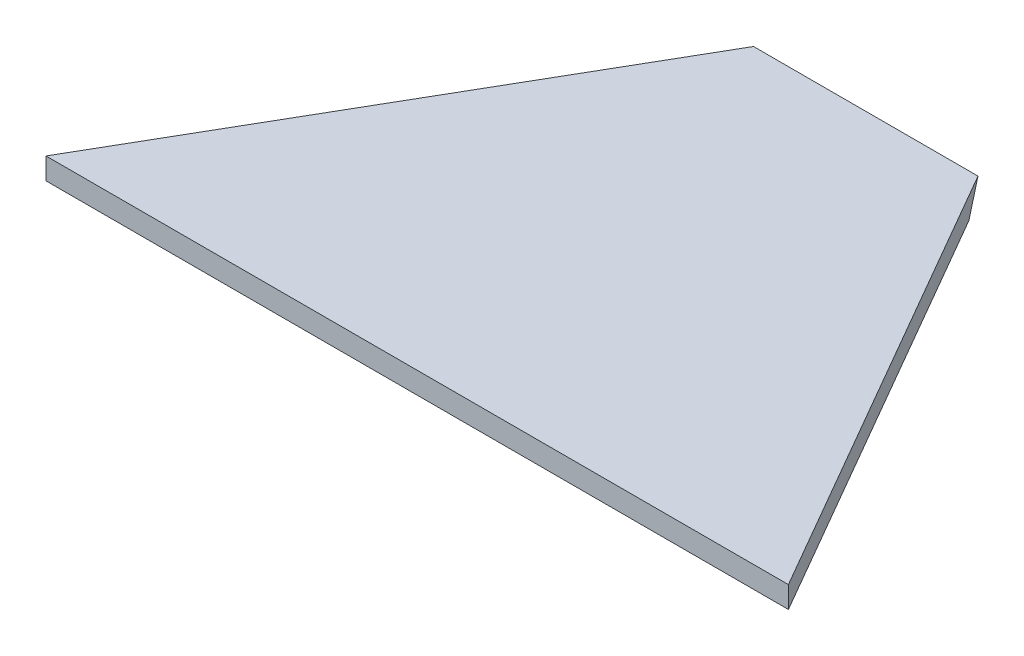
SolidWorks part; units mm, degrees
ref_plane "Front Plane" through (0, 0, 0) normal (0, 0, 1) x (1, 0, 0)
ref_plane "Top Plane" through (0, 0, 0) normal (0, 1, 0) x (1, 0, 0)
ref_plane "Right Plane" through (0, 0, 0) normal (1, 0, 0) x (0, 0, -1)
sketch "Sketch2" plane through (0, 0, 0) normal (0, 1, 0) x (1, 0, 0)
  line L0 (-109.22, -85.0861) -> (-33.02, 46.8961)
  line L1 (-33.02, 46.8961) -> (33.02, 46.8961)
  line L2 (0, 46.8961) -> (0, -85.0861) construction
  line L3 (-109.22, -85.0861) -> (109.22, -85.0861)
  line L4 (109.22, -85.0861) -> (33.02, 46.8961)
  dimension "D1" = 66.04
  dimension "D2" = 60
  dimension "D3" = 152.4
extrude "Boss-Extrude1" add sketch "Sketch2" along normal blind 6.35 contours L3 L4 L1 L0
sketch "Sketch4" plane through (0, 0, 0) normal (1, 0, 0) x (0, 0, -1)
  line L0 (46.8961, 6.35) -> (40.5461, 0)
  line L1 (-85.0861, 0) -> (46.8961, 0) construction
  line L2 (40.5461, 0) -> (46.8961, 0)
  line L3 (46.8961, 0) -> (46.8961, 6.35)
  dimension "D1" = 45
extrude "Cut-Extrude1" cut sketch "Sketch4" against normal up to next and the other way up to next
